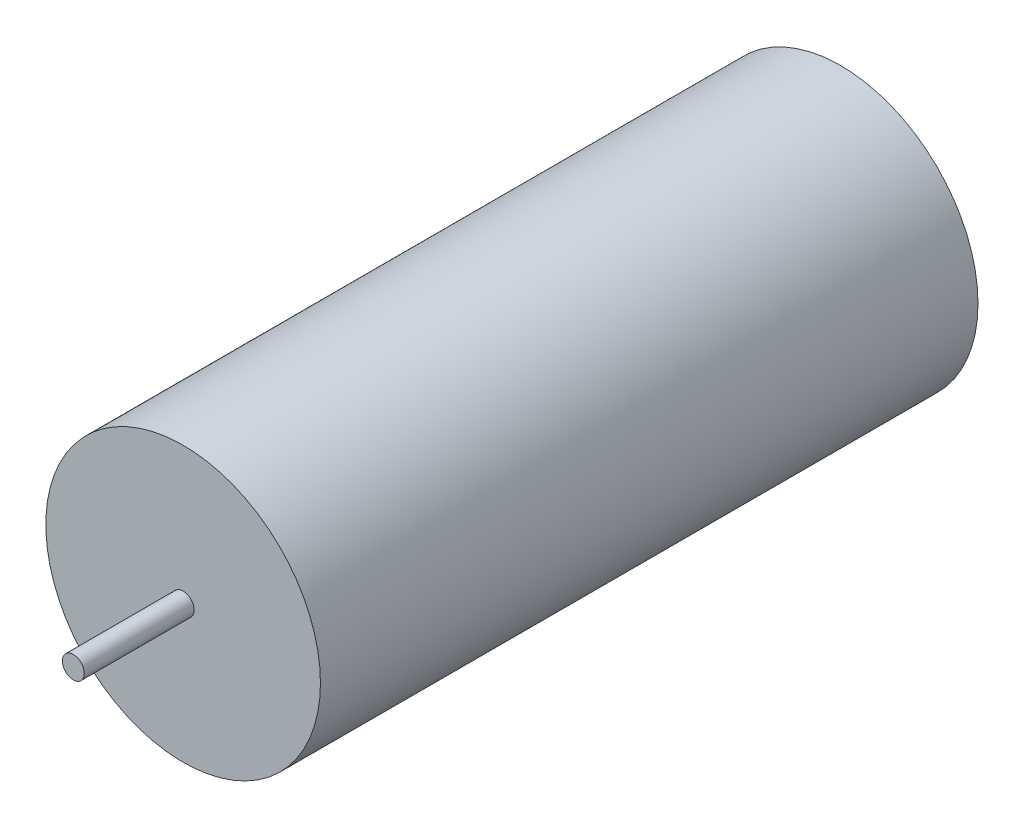
SolidWorks part; units mm, degrees
material "Brass"
ref_plane "Front Plane" through (0, 0, 0) normal (0, 0, 1) x (1, 0, 0)
ref_plane "Top Plane" through (0, 0, 0) normal (0, 1, 0) x (1, 0, 0)
ref_plane "Right Plane" through (0, 0, 0) normal (1, 0, 0) x (0, 0, -1)
sketch "Sketch1" plane through (0, 0, 0) normal (0, 0, 1) x (1, 0, 0)
  circle A0 centre (0, 0) radius 12.5
  dimension "D1" = 25
extrude "Boss-Extrude1" add sketch "Sketch1" along normal blind 59.86
sketch "Sketch2" plane through (0, 0, 59.86) normal (0, 0, 1) x (1, 0, 0)
  circle A0 centre (0, 0) radius 1
  dimension "D1" = 2
extrude "Boss-Extrude2" add sketch "Sketch2" along normal blind 10
